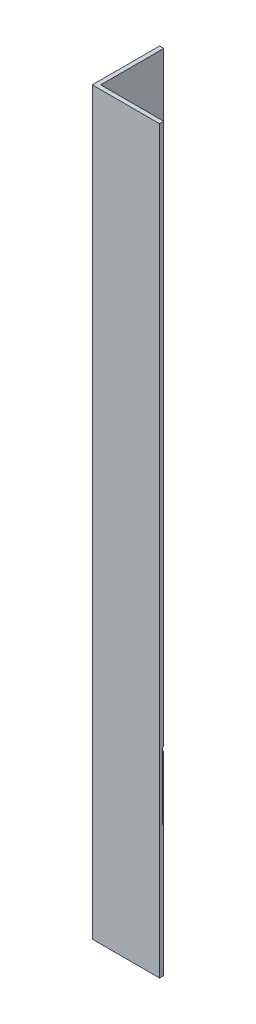
SolidWorks part; units mm, degrees
ref_plane "Front Plane" through (0, 0, 0) normal (0, 0, 1) x (1, 0, 0)
ref_plane "Top Plane" through (0, 0, 0) normal (0, 1, 0) x (1, 0, 0)
ref_plane "Right Plane" through (0, 0, 0) normal (1, 0, 0) x (0, 0, -1)
sketch "Sketch1" plane through (0, 0, 0) normal (0, 1, 0) x (1, 0, 0)
  line L0 (0, 0) -> (0, 25.4)
  line L1 (0, 25.4) -> (1.5875, 25.4)
  line L2 (1.5875, 25.4) -> (1.5875, 1.5875)
  line L3 (1.5875, 1.5875) -> (25.4, 1.5875)
  line L4 (25.4, 1.5875) -> (25.4, 0)
  line L5 (25.4, 0) -> (0, 0)
  dimension "D1" = 1.5875
  dimension "D2" = 25.4
extrude "Boss-Extrude1" add sketch "Sketch1" along normal blind 279.4
sketch "Sketch4" plane through (0, 0, 0) normal (-1, 0, 0) x (0, 0, 1)
  line L0 (-25.4, 279.4) -> (-25.4, 0) construction
  line L1 (-25.4, 49.6189) -> (-1.0841, 49.6189)
  line L2 (-25.4, 49.6189) -> (-25.4, 75.0189)
  line L3 (-25.4, 75.0189) -> (-1.0841, 75.0189)
  line L4 (-1.0841, 49.6189) -> (-1.0841, 75.0189)
  line L5 (-25.4, 0) -> (0, 0) construction
  line L6 (0, 279.4) -> (0, 0) construction
  dimension "D1" = 25.4
  dimension "D2" = 49.6189
  dimension "D3" = 1.0841
extrude "Cut-Extrude1" cut sketch "Sketch4" against normal through all
